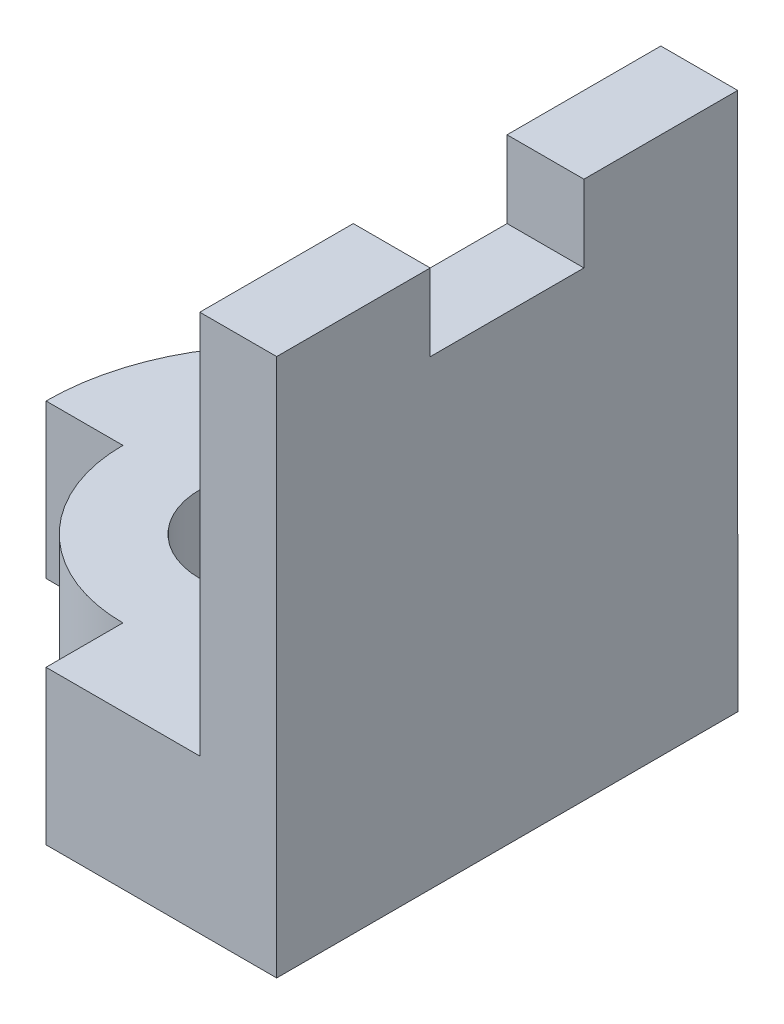
SolidWorks part; units mm, degrees
ref_plane "Front" through (0, 0, 0) normal (0, 0, 1) x (1, 0, 0)
ref_plane "Top" through (0, 0, 0) normal (0, 1, 0) x (1, 0, 0)
ref_plane "Right" through (0, 0, 0) normal (1, 0, 0) x (0, 0, -1)
sketch "Sketch1" plane through (0, 0, 0) normal (0, 1, 0) x (1, 0, 0)
  line L0 (0, -2) -> (0, -3)
  line L1 (-2, 0) -> (-3, 0)
  line L2 (0, -3) -> (3, -3)
  line L3 (0, 3) -> (3, 3)
  line L4 (3, 3) -> (3, -3)
  arc A0 (0, 3) -> (-3, 0) centre (0, 0) ccw
  circle A1 centre (0, 0) radius 1
  arc A2 (-2, 0) -> (0, -2) centre (0, 0) ccw
  point P1 (0, 3)
  dimension "D1" = 2
  dimension "D2" = 6
  dimension "D3" = 3
  dimension "D4" = 3
  dimension "D5" = 6
extrude "Boss-Extrude1" add sketch "Sketch1" along normal blind 2
sketch "Sketch3" plane through (3, 0, 0) normal (1, 0, 0) x (0, 0, -1)
  line L0 (0.9966, 7) -> (2.9966, 7)
  line L1 (-3, 2) -> (2.9966, 2)
  line L2 (-3, 2) -> (-3, 7)
  line L3 (-3, 7) -> (-1.0034, 7)
  line L4 (2.9966, 2) -> (2.9966, 7)
  line L6 (-1.0034, 7) -> (-1.0034, 6)
  line L7 (-1.0034, 6) -> (0.9966, 6)
  line L8 (0.9966, 7) -> (0.9966, 6)
  dimension "D1" = 5
  dimension "D2" = 5.9966
  dimension "D3" = 2
  dimension "D4" = 1
  dimension "D5" = 2
extrude "Boss-Extrude2" add sketch "Sketch3" against normal blind 1
